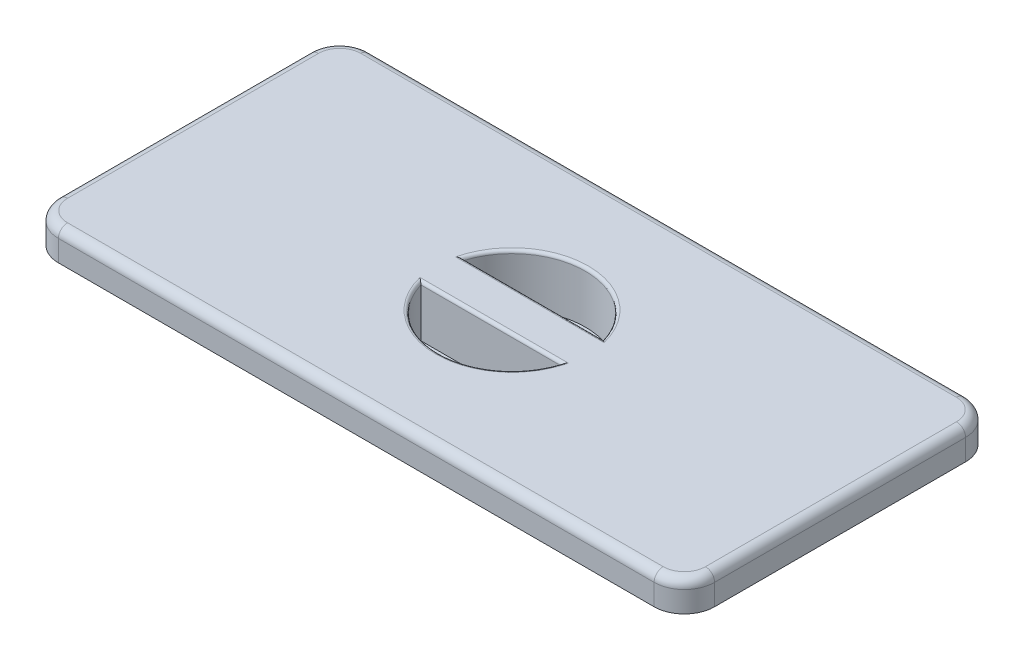
SolidWorks part; units mm, degrees
ref_plane "Front Plane" through (0, 0, 0) normal (0, 0, 1) x (1, 0, 0)
ref_plane "Top Plane" through (0, 0, 0) normal (0, 1, 0) x (1, 0, 0)
ref_plane "Right Plane" through (0, 0, 0) normal (1, 0, 0) x (0, 0, -1)
sketch "Sketch1" plane through (0, 0, 0) normal (0, 1, 0) x (1, 0, 0)
  line L1 (-108.5, -51.5) -> (108.5, -51.5)
  line L2 (-108.5, -51.5) -> (-108.5, 51.5)
  line L3 (-108.5, 51.5) -> (108.5, 51.5)
  line L4 (108.5, -51.5) -> (108.5, 51.5)
  line L5 (-108.5, -51.5) -> (108.5, 51.5) construction
  line L6 (-108.5, 51.5) -> (108.5, -51.5) construction
  point P0 (0, 0)
  dimension "D1" = 217
  dimension "D2" = 103
extrude "Boss-Extrude1" add sketch "Sketch1" along normal blind 10
fillet "Fillet1" radius 10 4 edges at (108.5, 5, 51.5) (108.5, 5, -51.5) (-108.5, 5, -51.5) (-108.5, 5, 51.5)
shell "Shell1" thickness 4
fillet "Fillet2" radius 3 8 edges at (-105.5711, 10, 48.5711) (-108.5, 10, 0) (-105.5711, 10, -48.5711) (0, 10, -51.5) (105.5711, 10, -48.5711) (108.5, 10, 0) (105.5711, 10, 48.5711) (0, 10, 51.5)
ref_plane "Plane1" through (0, -10, 0) normal (0, 1, 0) x (1, 0, 0)
sketch "Sketch4" plane through (0, 6, 0) normal (0, -1, 0) x (1, 0, 0)
  line L0 (-27.7048, 3.5) -> (27.7048, 3.5)
  line L1 (-27.7048, -3.5) -> (27.7048, -3.5)
  arc A0 (-27.7048, -3.5) -> (27.7048, -3.5) centre (0, 0) ccw
  arc A1 (27.7048, 3.5) -> (-27.7048, 3.5) centre (0, 0) ccw
  dimension "D1" = 55.85
  dimension "D2" = 7
sketch "Sketch2" plane through (0, 10, 0) normal (0, 1, 0) x (1, 0, 0)
  line L0 (-23.255, 6.875) -> (23.255, 6.875)
  line L1 (-23.255, -6.875) -> (23.255, -6.875)
  arc A0 (-23.255, -6.875) -> (23.255, -6.875) centre (0, 0) ccw
  arc A1 (23.255, 6.875) -> (-23.255, 6.875) centre (0, 0) ccw
  dimension "D1" = 48.5
  dimension "D2" = 13.75
extrude "Boss-Extrude3" add sketch "Sketch4" along normal up to surface (16 mm away) up to plane "Plane1"
extrude "Cut-Extrude2" cut sketch "Sketch2" against normal blind 17
fillet "Fillet3" radius 1 4 edges at (0, 10, 24.25) (0, 10, -24.25) (0, 10, -6.875) (0, 10, 6.875)
fillet "Fillet4" radius 1 12 edges at (0, 6, -3.5) (0, 6, 3.5) (-27.7048, -2, -3.5) (27.7048, -2, -3.5) (0, -10, -27.925) (0, 6, -27.925) (27.7048, -2, 3.5) (-27.7048, -2, 3.5) (0, -10, -3.5) (0, 6, 27.925) (0, -10, 27.925) (0, -10, 3.5)
sketch "Sketch5" plane through (0, 6, 0) normal (0, -1, 0) x (1, 0, 0)
  line L0 (-92.5, 36.425) -> (92.5, 36.425)
  line L1 (-92.5, 36.425) -> (-92.5, -36.425)
  line L2 (-92.5, -36.425) -> (92.5, -36.425)
  line L3 (92.5, -36.425) -> (92.5, -7.375)
  line L4 (92.5, 36.425) -> (92.5, 7.375)
  line L5 (92.5, -7.375) -> (92.5, 7.375) construction
  line L6 (-90.89, 34.325) -> (90.89, 34.325)
  line L7 (90.89, 34.325) -> (90.89, 7.375)
  line L8 (90.89, 7.375) -> (92.5, 7.375)
  line L9 (-90.89, 34.325) -> (-90.89, -34.325)
  line L10 (-90.89, -34.325) -> (90.89, -34.325)
  line L11 (90.89, -34.325) -> (90.89, -7.375)
  line L12 (90.89, -7.375) -> (92.5, -7.375)
  point P2 (92.5, 0)
  point P7 (-92.5, 0)
  point P8 (0, -36.425)
  point P10 (0, 36.425)
  dimension "D1" = 72.85
  dimension "D2" = 185
  dimension "D3" = 14.75
  dimension "D4" = 1.61
  dimension "D5" = 1.61
  dimension "D6" = 2.1
  dimension "D7" = 2.1
extrude "Boss-Extrude4" add sketch "Sketch5" along normal blind 8
fillet "Fillet5" radius 3 8 edges at (92.5, 2, 36.425) (90.89, 2, 34.325) (92.5, 2, -36.425) (90.89, 2, -34.325) (-90.89, 2, -34.325) (-92.5, 2, -36.425) (-90.89, 2, 34.325) (-92.5, 2, 36.425)
